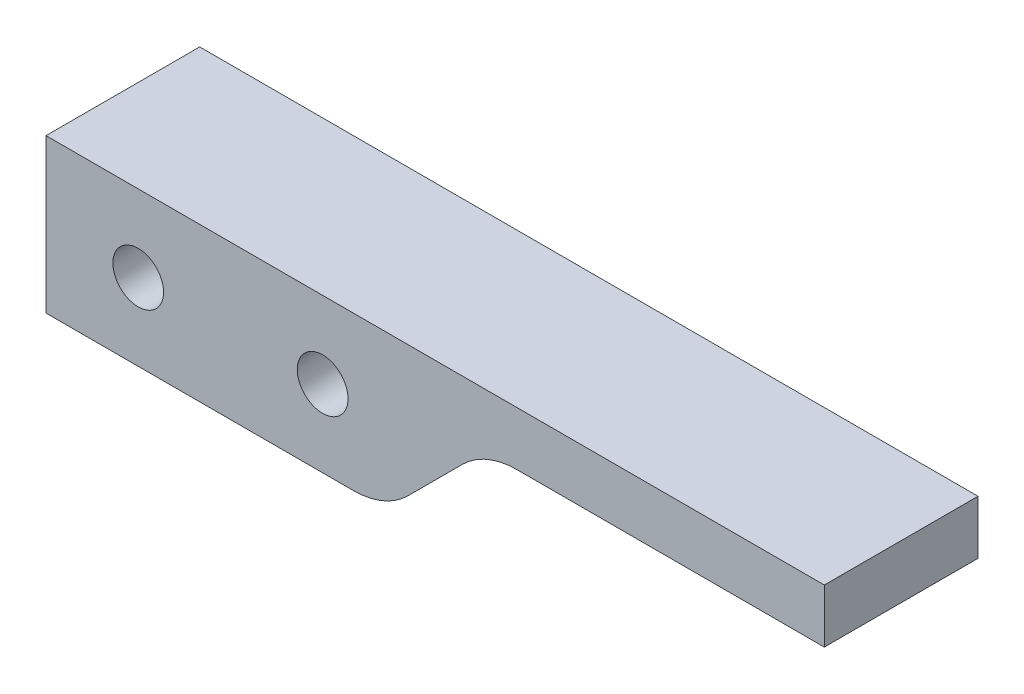
SolidWorks part; units mm, degrees
ref_plane "前视基准面" through (0, 0, 0) normal (0, 0, 1) x (1, 0, 0)
ref_plane "上视基准面" through (0, 0, 0) normal (0, 1, 0) x (1, 0, 0)
ref_plane "右视基准面" through (0, 0, 0) normal (1, 0, 0) x (0, 0, -1)
sketch "草图5" plane through (0, 0, 0) normal (0, 0, 1) x (1, 0, 0)
  line L0 (7865.358, 51.1708) -> (7885.358, 51.1708)
  line L1 (7858.2514, 46.1353) -> (7861.8225, 49.7064)
  line L2 (7834.7159, 44.6708) -> (7854.7159, 44.6708)
  line L3 (7834.7159, 54.6708) -> (7834.7159, 44.6708)
  line L4 (7885.358, 54.6708) -> (7834.7159, 54.6708)
  line L5 (7885.358, 51.1708) -> (7885.358, 54.6708)
  line L6 (7838.5159, 49.6708) -> (7842.9159, 49.6708) construction
  line L7 (7840.7159, 47.4708) -> (7840.7159, 51.8708) construction
  line L8 (7850.5159, 49.6708) -> (7854.9159, 49.6708) construction
  line L9 (7852.7159, 47.4708) -> (7852.7159, 51.8708) construction
  arc A0 (7865.358, 51.1708) -> (7861.8225, 49.7064) centre (7865.358, 46.1708) ccw
  arc A1 (7854.7159, 44.6708) -> (7858.2514, 46.1353) centre (7854.7159, 49.6708) ccw
  line B0 (7840.7159, 47.4708) -> (7840.7159, 51.8708) construction
  line B1 (7852.7159, 47.4708) -> (7852.7159, 51.8708) construction
sketch_block_instance "SCREW_M4_L-3"
sketch_block "SCREW_M4_L"
sketch_block_instance "SCREW_M4_L-4"
extrude "凸台-拉伸1" add sketch "草图5" along normal blind 10 contours L2 A1 L1 A0 L0 L5 L4 L3
hole_wizard "M4 螺纹孔1" positions "草图7" profile "草图8" tap size "M4" standard "ISO" end condition through all
sketch "草图7" plane through (0, 0, 10) normal (0, 0, 1) x (1, 0, 0)
  line L0 (7885.358, 54.6708) -> (7834.7159, 54.6708) construction
  line L1 (7834.7159, 54.6708) -> (7834.7159, 44.6708) construction
  point P0 (7840.7159, 49.6708)
  point P2 (7852.7159, 49.6708)
  dimension "D1" = 5
  dimension "D2" = 18
  dimension "D3" = 6
cosmetic thread "孔螺蚊线1"
cosmetic thread "孔螺蚊线2"
sketch "草图8" plane through (7840.7159, 49.6708, 10) normal (1, 0, 0) x (0, -1, 0)
  line L0 (0, 0) -> (0, 10)
  line L1 (0, 10) -> (1.65, 10)
  line L2 (1.65, 10) -> (1.65, 0)
  line L5 (1.65, 0) -> (0, 0)
  line L11 (0, -6.35) -> (0, 107.95) construction
  dimension "通孔螺纹孔钻头直径" = 3.3
  dimension "通孔螺纹孔钻头深度" = 10
